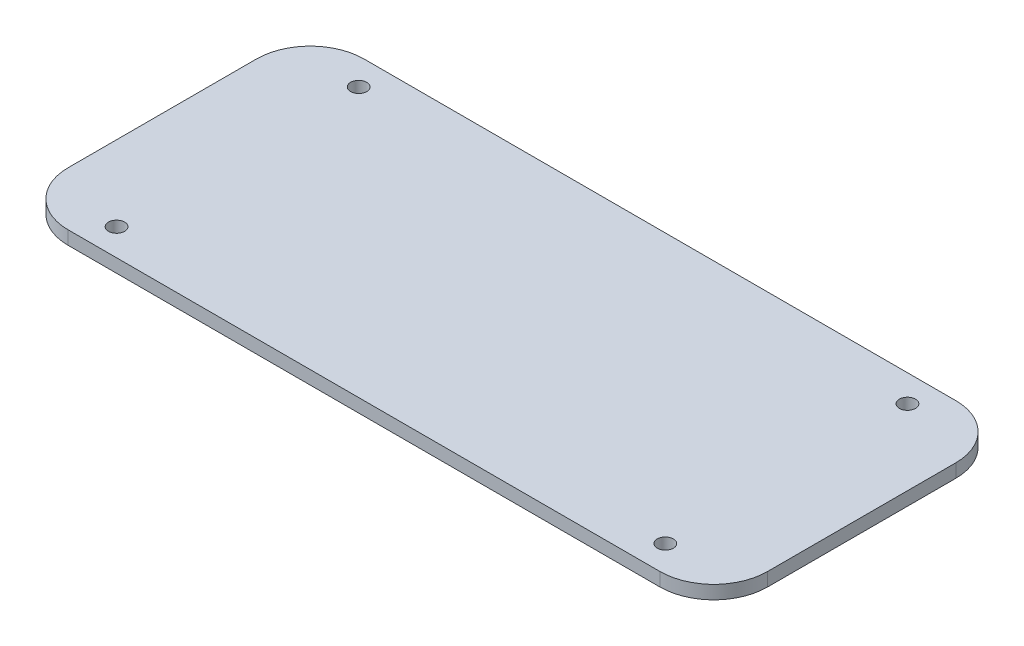
SolidWorks part; units mm, degrees
ref_plane "Front Plane" through (0, 0, 0) normal (0, 0, 1) x (1, 0, 0)
ref_plane "Top Plane" through (0, 0, 0) normal (0, 1, 0) x (1, 0, 0)
ref_plane "Right Plane" through (0, 0, 0) normal (1, 0, 0) x (0, 0, -1)
sketch "Sketch1" plane through (0, 0, 0) normal (0, 1, 0) x (1, 0, 0)
  line L1 (10, 0) -> (120, 0)
  line L2 (0, 10) -> (0, 45)
  line L3 (10, 55) -> (120, 55)
  line L4 (130, 10) -> (130, 45)
  arc A0 (10, 55) -> (0, 45) centre (10, 45) ccw
  arc A1 (0, 10) -> (10, 0) centre (10, 10) ccw
  arc A2 (130, 10) -> (120, 0) centre (120, 10) cw
  arc A3 (120, 55) -> (130, 45) centre (120, 45) cw
  point P7 (0, 55)
  point P10 (0, 0)
  point P13 (130, 0)
  dimension "D3" = 10
  dimension "D4" = 10
  dimension "D5" = 10
  dimension "D6" = 10
  dimension "D1" = 130
  dimension "D2" = 55
extrude "Boss-Extrude1" add sketch "Sketch1" along normal blind 2.5
sketch "Sketch2" plane through (0, 2.5, 0) normal (0, 1, 0) x (1, 0, 0)
  line L0 (0, 45) -> (0, 10) construction
  line L1 (10, 0) -> (120, 0) construction
  line L2 (120, 55) -> (10, 55) construction
  line L3 (65, 55) -> (65, 0) construction
  circle A0 centre (14, 5) radius 1.5
  circle A1 centre (14, 50) radius 1.5
  circle A2 centre (116, 5) radius 1.5
  circle A3 centre (116, 50) radius 1.5
  dimension "D1" = 3
  dimension "D4" = 3
  dimension "D2" = 14
  dimension "D3" = 5
  dimension "D5" = 5
extrude "Cut-Extrude1" cut sketch "Sketch2" against normal through all
